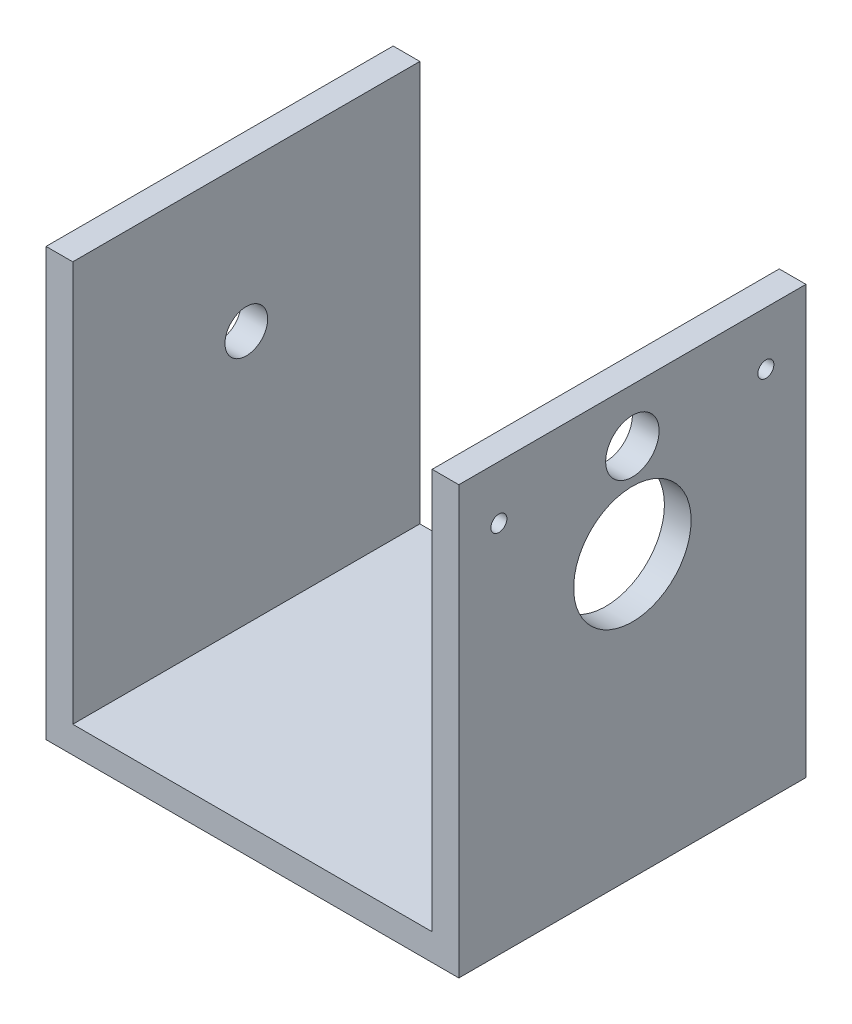
SolidWorks part; units mm, degrees
ref_plane "Ön Düzlem" through (0, 0, 0) normal (0, 0, 1) x (1, 0, 0)
ref_plane "Üst Düzlem" through (0, 0, 0) normal (0, 1, 0) x (1, 0, 0)
ref_plane "Sağ Düzlem" through (0, 0, 0) normal (1, 0, 0) x (0, 0, -1)
sketch "Sketch1" plane through (0, 0, 0) normal (1, 0, 0) x (0, 0, -1)
  line L0 (-17.5, 27.5) -> (-27.5, 27.5)
  line L1 (-17.5, 27.5) -> (17.5, 27.5)
  line L2 (-27.5, 17.5) -> (-27.5, -27.5)
  line L3 (-27.5, -27.5) -> (37.5, -27.5)
  line L4 (37.5, 7.5) -> (37.5, -27.5)
  line L5 (37.5, 27.5) -> (-27.5, -27.5) construction
  line L6 (-27.5, 27.5) -> (37.5, -27.5) construction
  line L7 (37.5, 7.5) -> (37.5, 27.5)
  line L8 (37.5, 27.5) -> (17.5, 27.5)
  line L9 (-27.5, 27.5) -> (-27.5, 17.5)
  circle A0 centre (5, 0) radius 11
  circle A1 centre (5, 17.5) radius 5
  circle A2 centre (30, 17.5) radius 1.5
  circle A3 centre (-20, 17.5) radius 1.5
  dimension "D1" = 22
  dimension "D2" = 17.5
  dimension "D3" = 10
  dimension "D4" = 3
  dimension "D5" = 3
  dimension "D6" = 50
  dimension "D7" = 25
  dimension "D8" = 65
extrude "Boss-Extrude1" add sketch "Sketch1" along normal blind 5
sketch "Sketch2" plane through (0, -27.5, 0) normal (0, -1, 0) x (1, 0, 0)
  line L1 (0, 27.5) -> (5, 27.5)
  line L2 (0, 27.5) -> (0, -37.5)
  line L3 (0, -37.5) -> (5, -37.5)
  line L4 (5, 27.5) -> (5, -37.5)
extrude "Boss-Extrude2" add sketch "Sketch2" along normal blind 25
sketch "Sketch3" plane through (0, -52.5, 0) normal (0, -1, 0) x (1, 0, 0)
  line L1 (0, 27.5) -> (-72.3, 27.5)
  line L2 (0, 27.5) -> (0, -37.5)
  line L3 (0, -37.5) -> (-72.3, -37.5)
  line L4 (-72.3, 27.5) -> (-72.3, -37.5)
  dimension "D1" = 72.3
  dimension "D2" = 65
extrude "Boss-Extrude3" add sketch "Sketch3" against normal blind 5
sketch "Sketch4" plane through (-72.3, 0, 0) normal (-1, 0, 0) x (0, 0, 1)
  line L1 (-37.5, -47.5) -> (27.5, -47.5)
  line L2 (27.5, -47.5) -> (27.5, 27.5)
  line L3 (27.5, 27.5) -> (-37.5, 27.5)
  line L4 (-37.5, 27.5) -> (-37.5, -47.5)
  circle A0 centre (-5, 0) radius 4
  dimension "D2" = 8
  dimension "D1" = 75
extrude "Boss-Extrude4" add sketch "Sketch4" against normal blind 5
